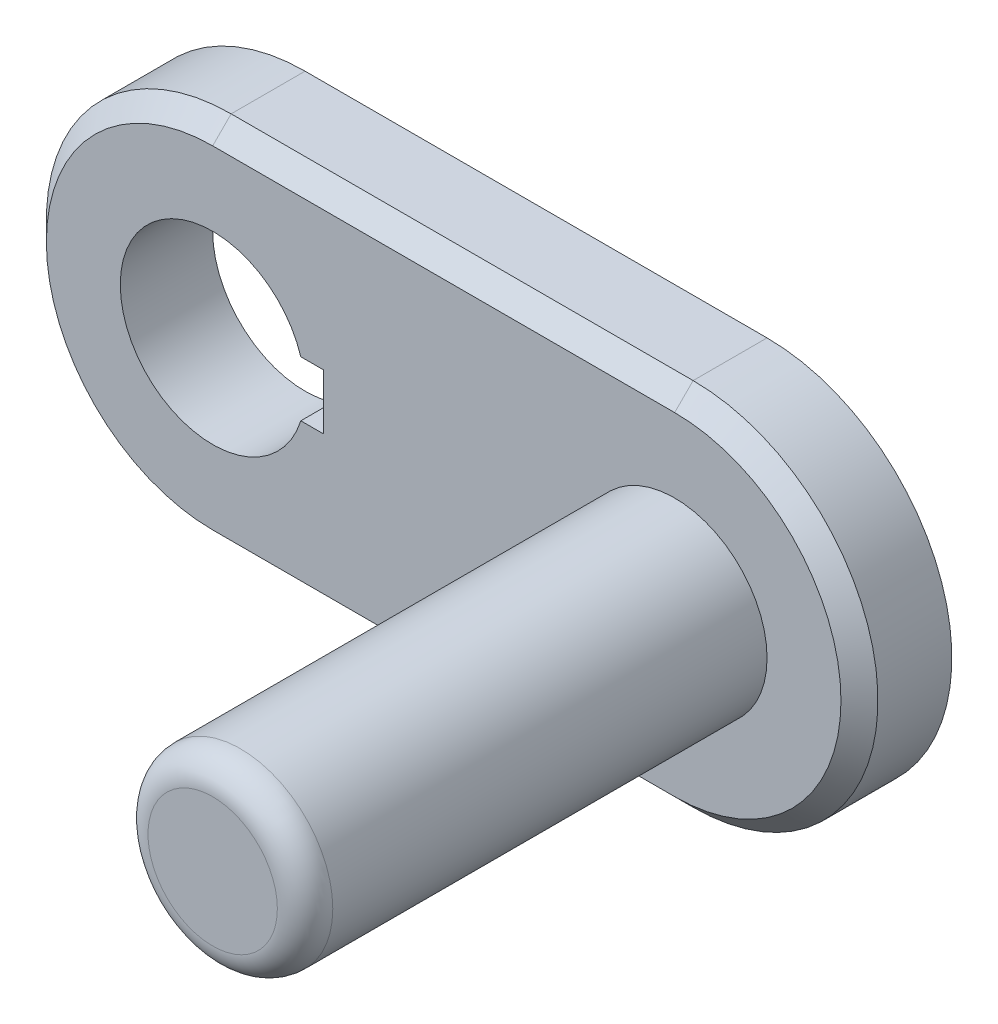
SolidWorks part; units mm, degrees
ref_plane "Front Plane" through (0, 0, 0) normal (0, 0, 1) x (1, 0, 0)
ref_plane "Top Plane" through (0, 0, 0) normal (0, 1, 0) x (1, 0, 0)
ref_plane "Right Plane" through (0, 0, 0) normal (1, 0, 0) x (0, 0, -1)
sketch "Sketch1" plane through (0, 0, 0) normal (0, 0, 1) x (1, 0, 0)
  line L0 (0, 0) -> (50, 0) construction
  line L1 (0, 20) -> (50, 20)
  line L2 (0, -20) -> (50, -20)
  line L4 (9.5394, 3) -> (12, 3)
  line L6 (9.5394, -3) -> (12, -3)
  line L7 (12, 3) -> (12, -3)
  arc A0 (0, 20) -> (0, -20) centre (0, 0) ccw
  arc A1 (50, -20) -> (50, 20) centre (50, 0) ccw
  arc A2 (9.5394, 3) -> (9.5394, -3) centre (0, 0) ccw
  point P3 (25, 0)
  point P15 (12, 0)
  dimension "D2" = 20
  dimension "D5" = 10
  dimension "D1" = 50
  dimension "D3" = 12
  dimension "D4" = 6
extrude "Boss-Extrude1" add sketch "Sketch1" along normal blind 10
sketch "Sketch2" plane through (0, 0, 10) normal (0, 0, 1) x (1, 0, 0)
  circle A0 centre (50, 0) radius 10
extrude "Boss-Extrude2" add sketch "Sketch2" along normal blind 50
fillet "Fillet1" radius 3 1 edges at (60, 0, 60)
chamfer "Chamfer1" distance 2 angle 45 4 edges at (70, 0, 10) (25, 20, 10) (-20, 0, 10) (25, -20, 10)
